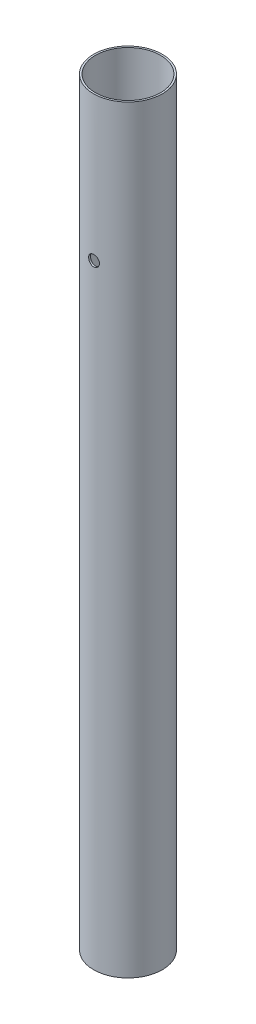
SolidWorks part; units mm, degrees
ref_plane "Front Plane" through (0, 0, 0) normal (0, 0, 1) x (1, 0, 0)
ref_plane "Top Plane" through (0, 0, 0) normal (0, 1, 0) x (1, 0, 0)
ref_plane "Right Plane" through (0, 0, 0) normal (1, 0, 0) x (0, 0, -1)
sketch "Sketch1" plane through (0, 0, 0) normal (0, 1, 0) x (1, 0, 0)
  circle A0 centre (0, 0) radius 9.5
  circle A1 centre (0, 0) radius 9
  dimension "D1" = 19
  dimension "D2" = 18
extrude "Boss-Extrude1" add sketch "Sketch1" along normal blind 210
sketch "Sketch2" plane through (0, 0, 0) normal (0, 0, 1) x (1, 0, 0)
  line L0 (9, 210) -> (-9, 210) construction
  circle A0 centre (0, 170) radius 1.5
  dimension "D1" = 3
  dimension "D2" = 40
extrude "Cut-Extrude1" cut sketch "Sketch2" against normal through all both and the other way through all
